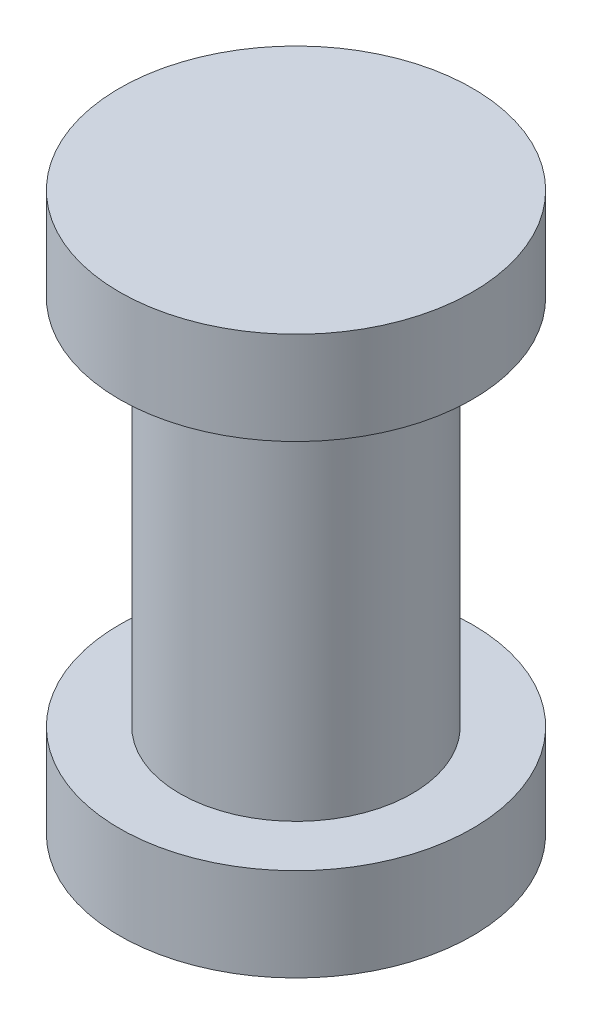
SolidWorks part; units mm, degrees
ref_plane "Front Plane" through (0, 0, 0) normal (0, 0, 1) x (1, 0, 0)
ref_plane "Top Plane" through (0, 0, 0) normal (0, 1, 0) x (1, 0, 0)
ref_plane "Right Plane" through (0, 0, 0) normal (1, 0, 0) x (0, 0, -1)
sketch "Sketch1" plane through (0, 0, 0) normal (0, 1, 0) x (1, 0, 0)
  line L0 (0, 18.8268) -> (0, -19.4528) construction
  line L1 (-54.1996, 0) -> (61.7124, 0) construction
  circle A0 centre (0, 0) radius 19
  dimension "D1" = 38
extrude "Boss-Extrude1" add sketch "Sketch1" against normal blind 10
sketch "Sketch2" plane through (0, -10, 0) normal (0, -1, 0) x (1, 0, 0)
  circle A0 centre (0, 0) radius 12.5
  dimension "D1" = 25
extrude "Boss-Extrude2" add sketch "Sketch2" along normal blind 50
sketch "Sketch4" plane through (0, -60, 0) normal (0, -1, 0) x (1, 0, 0)
  circle A0 centre (0, 0) radius 19
  dimension "D1" = 38
extrude "Boss-Extrude3" add sketch "Sketch4" against normal blind 10
